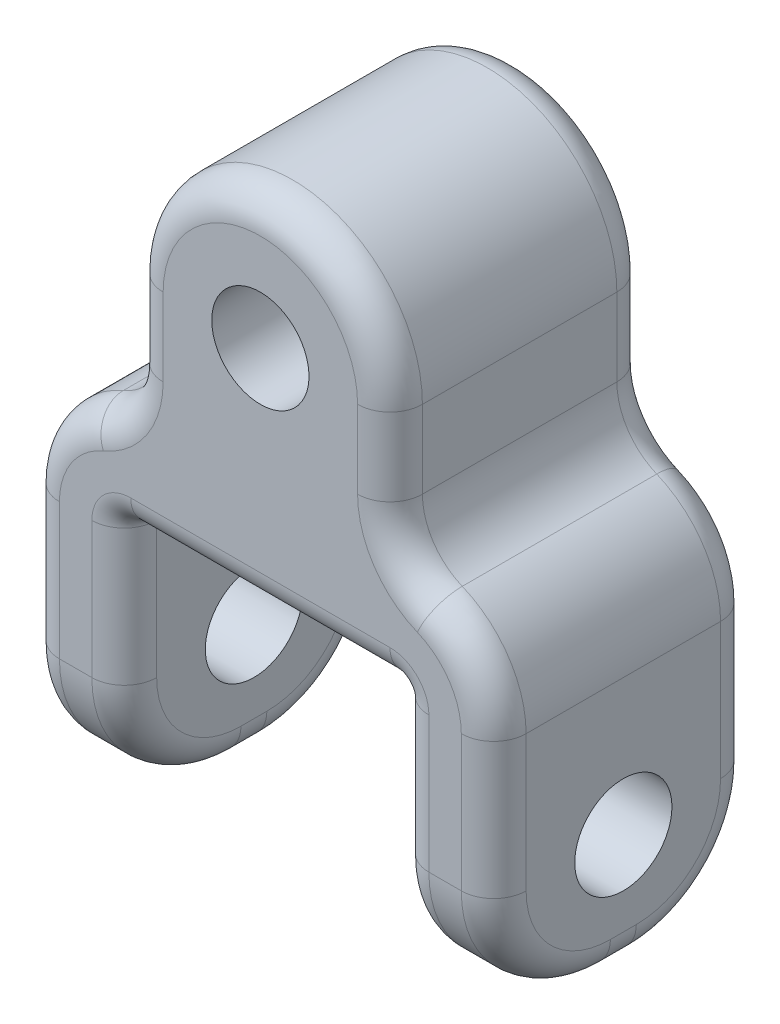
SolidWorks part; units mm, degrees
ref_plane "Front Plane" through (0, 0, 0) normal (0, 0, 1) x (1, 0, 0)
ref_plane "Top Plane" through (0, 0, 0) normal (0, 1, 0) x (1, 0, 0)
ref_plane "Right Plane" through (0, 0, 0) normal (1, 0, 0) x (0, 0, -1)
ref_plane "Plane2" through (0, 0, -272.5) normal (0, 0, 1) x (1, 0, 0)
sketch "Sketch7" plane through (0, 0, 0) normal (0, 0, 1) x (1, 0, 0)
  line L0 (-21, 40) -> (21, 40)
  line L1 (21, 40) -> (21, 0)
  line L2 (21, 0) -> (36, 0)
  line L3 (36, 0) -> (36, 39)
  line L4 (20, 63) -> (20, 75)
  line L5 (-20, 75) -> (-20, 63)
  line L6 (-36, 39) -> (-36, 0)
  line L7 (-36, 0) -> (-21, 0)
  line L8 (-21, 0) -> (-21, 40)
  line L9 (-36, 0) -> (36, 0) construction
  line L10 (0, 40) -> (0, 0) construction
  arc A0 (36, 39) -> (26.1538, 53.7692) centre (20, 39) ccw
  arc A1 (26.1538, 53.7692) -> (20, 63) centre (30, 63) cw
  arc A2 (20, 75) -> (-20, 75) centre (0, 75) ccw
  arc A3 (-20, 63) -> (-26.1538, 53.7692) centre (-30, 63) cw
  arc A4 (-26.1538, 53.7692) -> (-36, 39) centre (-20, 39) ccw
  dimension "D4" = 20
  dimension "D9" = 10
  dimension "D10" = 16
  dimension "D1" = 72
  dimension "D2" = 42
  dimension "D3" = 75
  dimension "D5" = 63
  dimension "D6" = 30
  dimension "D7" = 20
  dimension "D8" = 39
  dimension "D11" = 40
extrude "Boss-Extrude2" add sketch "Sketch7" against normal blind 40 separate body
fillet "Fillet4" radius 18 4 edges at (-28.5, 0, -40) (28.5, 0, -40) (-28.5, 0, 0) (28.5, 0, 0)
sketch "Sketch8" plane through (36, 0, 0) normal (1, 0, 0) x (0, 0, -1)
  line L0 (20, 0) -> (20, 247.8744) construction
  line L1 (22, 0) -> (18, 0) construction
  circle A0 centre (20, 18) radius 7.5
  point P7 (18, 18)
  dimension "D1" = 15
extrude "Cut-Extrude3" cut sketch "Sketch8" against normal through all
sketch "Sketch9" plane through (0, 0, -40) normal (0, 0, -1) x (-1, 0, 0)
  circle A0 centre (0, 75) radius 7.5
  dimension "D1" = 15
extrude "Cut-Extrude4" cut sketch "Sketch9" against normal through all
fillet "Fillet5" radius 1 2 edges at (-21, 40, -20) (21, 40, -20)
fillet "Fillet6" radius 5 40 edges at (-33.3128, 47.8752, 0) (-21.6795, 57.453, 0) (-36, 28.5, 0) (-20, 69, 0) (-36, 5.2721, -5.2721) (0, 95, 0) (-36, 0, -20) (20, 69, 0) (-36, 5.2721, -34.7279) (21.6795, 57.453, 0) (-36, 28.5, -40) (33.3128, 47.8752, 0) (-33.3128, 47.8752, -40) (36, 28.5, 0) (-21.6795, 57.453, -40) (36, 5.2721, -5.2721) (-20, 69, -40) (36, 0, -20) (0, 95, -40) (36, 5.2721, -34.7279) (20, 69, -40) (36, 28.5, -40) (21.6795, 57.453, -40) (33.3128, 47.8752, -40) (-21, 5.2721, -5.2721) (-21, 28.5, 0) (-21, 0, -20) (-20.7071, 39.7071, 0) (-21, 5.2721, -34.7279) (0, 40, 0) (-21, 28.5, -40) (20.7071, 39.7071, 0) (-20.7071, 39.7071, -40) (21, 28.5, 0) (0, 40, -40) (21, 5.2721, -5.2721) (20.7071, 39.7071, -40) (21, 28.5, -40) (21, 0, -20) (21, 5.2721, -34.7279)
